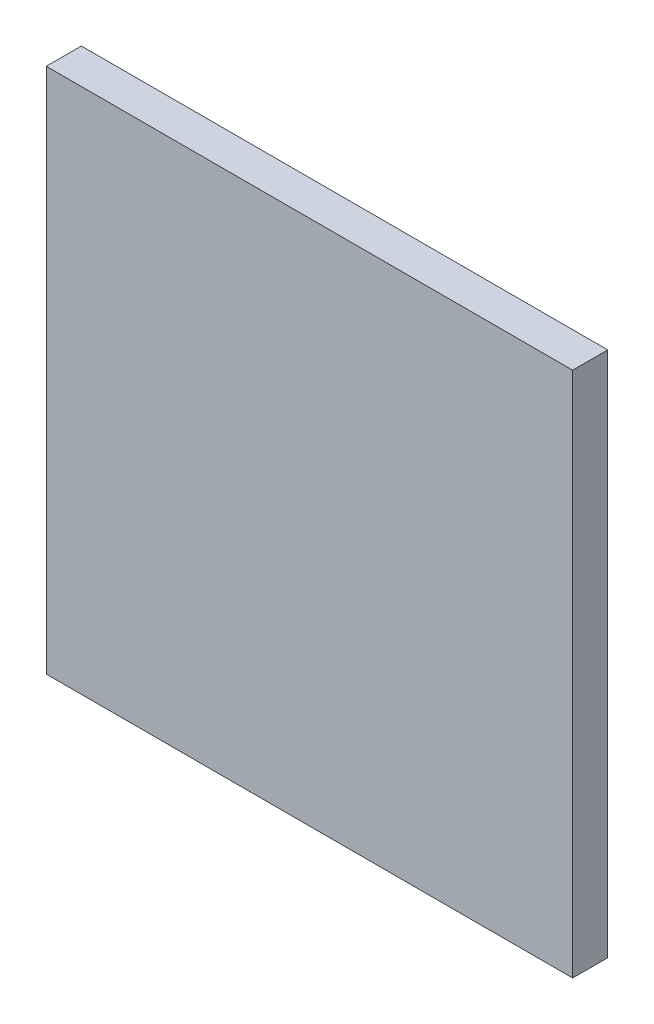
SolidWorks part; units mm, degrees
ref_plane "Front Plane" through (0, 0, 0) normal (0, 0, 1) x (1, 0, 0)
ref_plane "Top Plane" through (0, 0, 0) normal (0, 1, 0) x (1, 0, 0)
ref_plane "Right Plane" through (0, 0, 0) normal (1, 0, 0) x (0, 0, -1)
sketch "Sketch1" plane through (0, 0, 0) normal (0, 0, 1) x (1, 0, 0)
  line L1 (74.8235, -75) -> (-75.1765, -75)
  line L2 (74.8235, -75) -> (74.8235, 75)
  line L3 (74.8235, 75) -> (-75.1765, 75)
  line L4 (-75.1765, -75) -> (-75.1765, 75)
  dimension "D1" = 150
  dimension "D2" = 150
extrude "Boss-Extrude1" add sketch "Sketch1" along normal blind 10 contours L2 L1 L4 L3
